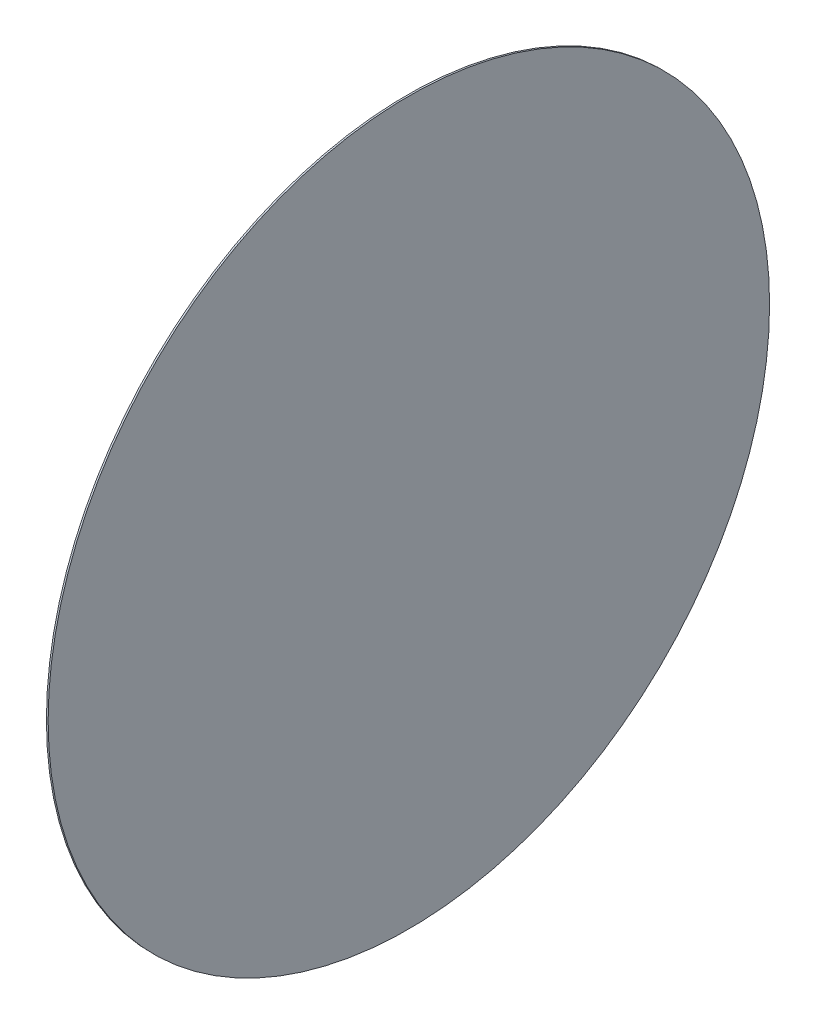
SolidWorks part; units mm, degrees
ref_plane "前视基准面" through (0, 0, 0) normal (0, 0, 1) x (1, 0, 0)
ref_plane "上视基准面" through (0, 0, 0) normal (0, 1, 0) x (1, 0, 0)
ref_plane "右视基准面" through (0, 0, 0) normal (1, 0, 0) x (0, 0, -1)
sketch "草图1" plane through (0, 0, 0) normal (0, 0, 1) x (1, 0, 0)
  line L0 (0, 9) -> (0, 0)
  line L2 (0, 9) -> (0.043, 9)
  line L3 (0, 0) -> (0.043, 0)
  line L4 (0.043, 9) -> (0.043, 0)
  dimension "D1" = 9
  dimension "D2" = 0.043
revolve "旋转2" add sketch "草图1" angle 360 about L3
